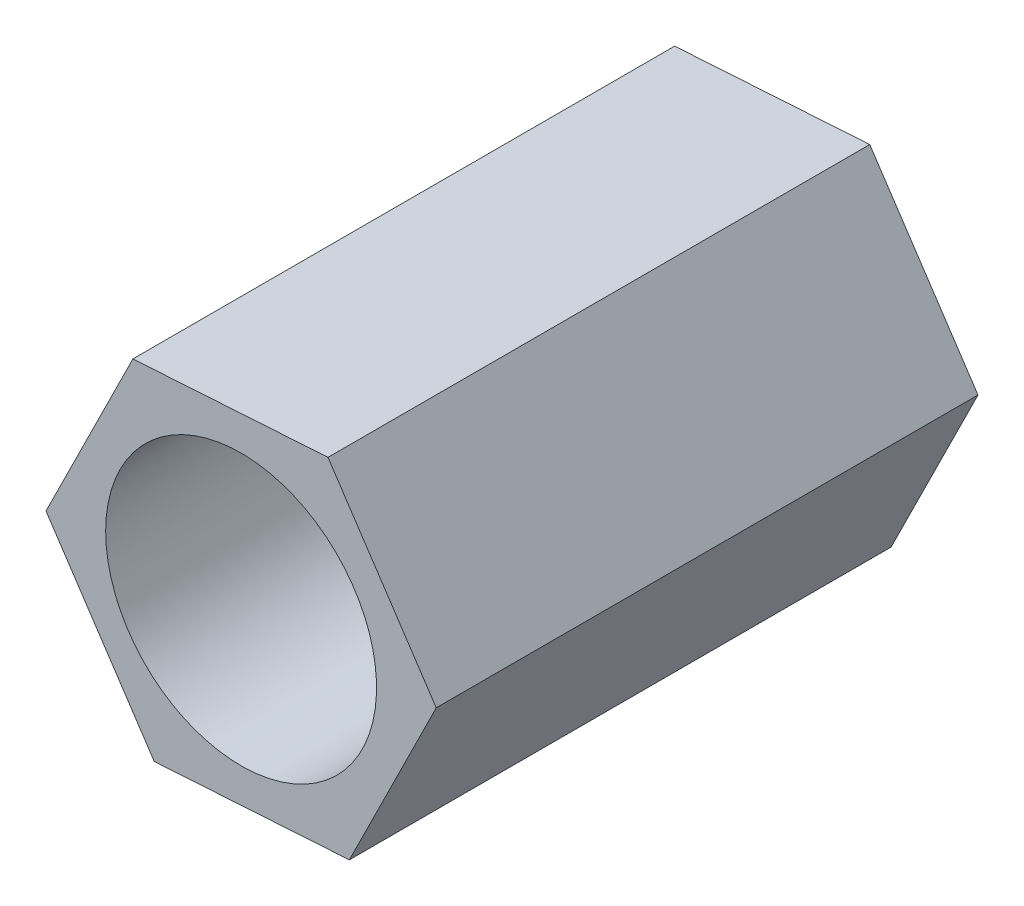
SolidWorks part; units mm, degrees
ref_plane "前视基准面" through (0, 0, 0) normal (0, 0, 1) x (1, 0, 0)
ref_plane "上视基准面" through (0, 0, 0) normal (0, 1, 0) x (1, 0, 0)
ref_plane "右视基准面" through (0, 0, 0) normal (1, 0, 0) x (0, 0, -1)
sketch "草图1" plane through (0, 0, 0) normal (0, 0, 1) x (1, 0, 0)
  line L1 (1.2828, 2.586) -> (-1.5982, 2.404)
  line L2 (-1.5982, 2.404) -> (-2.881, -0.182)
  line L3 (-2.881, -0.182) -> (-1.2828, -2.586)
  line L4 (-1.2828, -2.586) -> (1.5982, -2.404)
  line L5 (1.5982, -2.404) -> (2.881, 0.182)
  line L6 (2.881, 0.182) -> (1.2828, 2.586)
  circle A0 centre (0, 0) radius 2.5 construction
  dimension "D1" = 5
extrude "凸台-拉伸1" add sketch "草图1" along normal blind 8
sketch "草图2" plane through (0, 0, 0) normal (0, 0, -1) x (-1, 0, 0)
  circle A0 centre (0, 0) radius 2
  dimension "D1" = 4
extrude "切除-拉伸1" cut sketch "草图2" against normal through all
